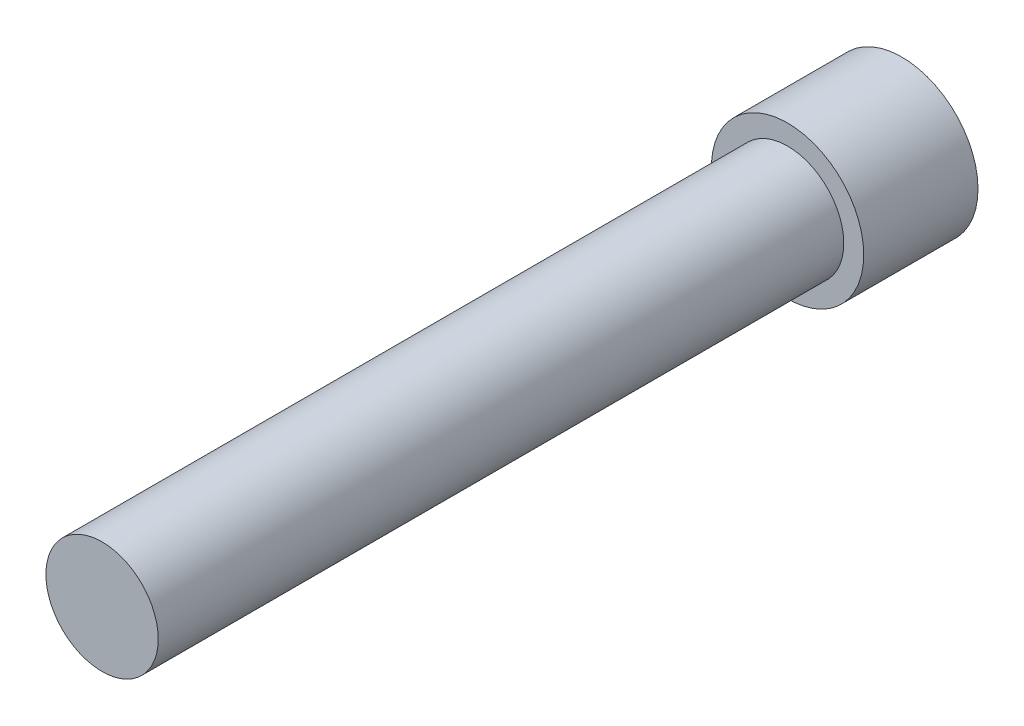
SolidWorks part; units mm, degrees
ref_plane "Front Plane" through (0, 0, 0) normal (0, 0, 1) x (1, 0, 0)
ref_plane "Top Plane" through (0, 0, 0) normal (0, 1, 0) x (1, 0, 0)
ref_plane "Right Plane" through (0, 0, 0) normal (1, 0, 0) x (0, 0, -1)
sketch "Sketch1" plane through (0, 0, 0) normal (0, 0, 1) x (1, 0, 0)
  circle A0 centre (0, 0) radius 2
extrude "Extrude1" add sketch "Sketch1" along normal blind 3
sketch "Sketch3" plane through (0, 0, 0) normal (0, 0, -1) x (-1, 0, 0)
  line L1 (-1.4434, 0) -> (-0.7217, -1.25)
  line L2 (-0.7217, -1.25) -> (0.7217, -1.25)
  line L3 (0.7217, -1.25) -> (1.4434, 0)
  line L4 (1.4434, 0) -> (0.7217, 1.25)
  line L5 (0.7217, 1.25) -> (-0.7217, 1.25)
  line L6 (-0.7217, 1.25) -> (-1.4434, 0)
  circle A0 centre (0, 0) radius 1.25 construction
extrude "Extrude3" cut sketch "Sketch3" against normal blind 1.82
sketch "Sketch2" plane through (0, 0, 3) normal (0, 0, 1) x (1, 0, 0)
  circle A0 centre (0, 0) radius 1.475
extrude "Extrude2" add sketch "Sketch2" along normal blind 18
